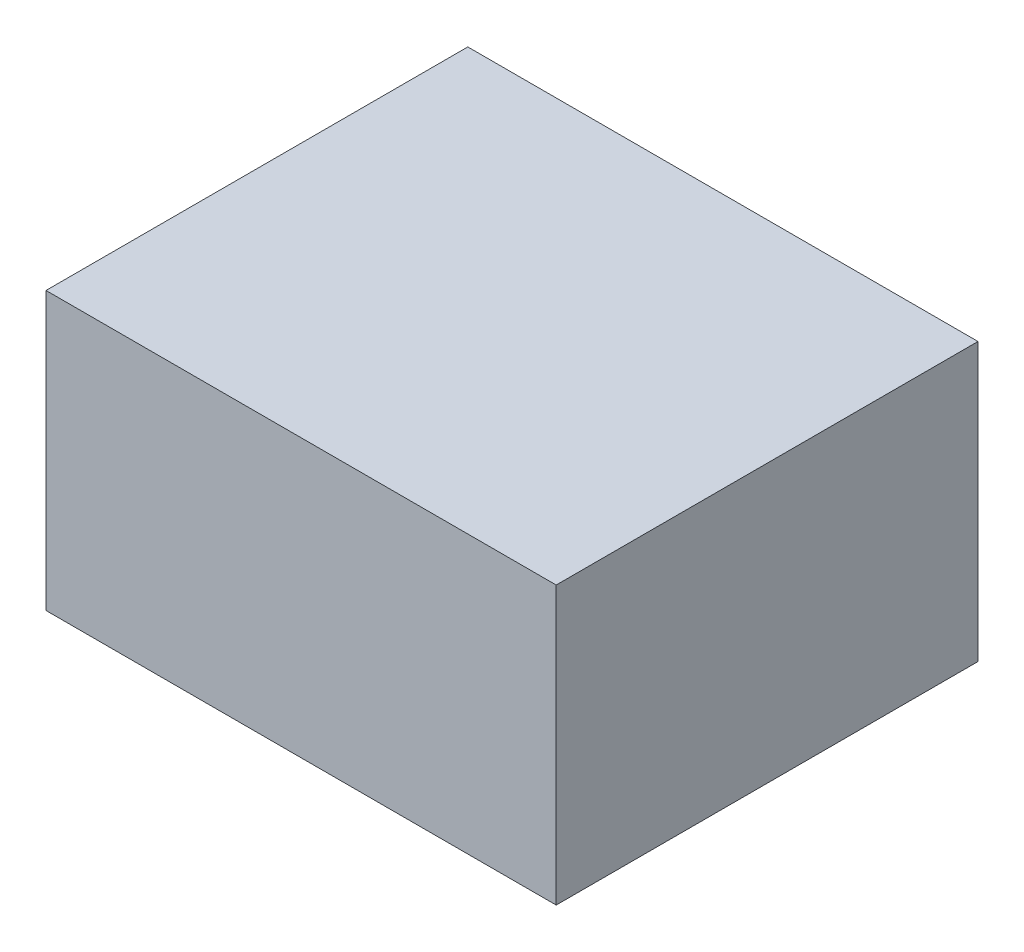
SolidWorks part; units mm, degrees
ref_plane "Front Plane" through (0, 0, 0) normal (0, 0, 1) x (1, 0, 0)
ref_plane "Top Plane" through (0, 0, 0) normal (0, 1, 0) x (1, 0, 0)
ref_plane "Right Plane" through (0, 0, 0) normal (1, 0, 0) x (0, 0, -1)
sketch "Sketch1" plane through (0, 0, 0) normal (0, 1, 0) x (1, 0, 0)
  line L1 (-81.6365, 40.3414) -> (40.3635, 40.3414)
  line L2 (-81.6365, 40.3414) -> (-81.6365, -59.6586)
  line L3 (-81.6365, -59.6586) -> (40.3635, -59.6586)
  line L4 (40.3635, 40.3414) -> (40.3635, -59.6586)
  line L5 (-84.1365, 42.8414) -> (42.8635, 42.8414)
  line L6 (-84.1365, 42.8414) -> (-84.1365, -62.1586)
  line L7 (-84.1365, -62.1586) -> (42.8635, -62.1586)
  line L8 (42.8635, 42.8414) -> (42.8635, -62.1586)
  dimension "D1" = 100
  dimension "D2" = 122
  dimension "D3" = 2.5
  dimension "D4" = 2.5
  dimension "D5" = 2.5
  dimension "D6" = 2.5
extrude "Boss-Extrude3" add sketch "Sketch1" along normal blind 66.5
sketch "Sketch4" plane through (0, 66.5, 0) normal (0, 1, 0) x (1, 0, 0)
  line L0 (42.8635, 42.8414) -> (-84.1365, 42.8414) construction
  line L1 (-84.1365, -62.1586) -> (42.8635, -62.1586)
  line L2 (-84.1365, -62.1586) -> (-84.1365, 42.8414)
  line L3 (-84.1365, 42.8414) -> (42.8635, 42.8414)
  line L4 (42.8635, -62.1586) -> (42.8635, 42.8414)
extrude "Boss-Extrude4" add sketch "Sketch4" along normal blind 2.5
